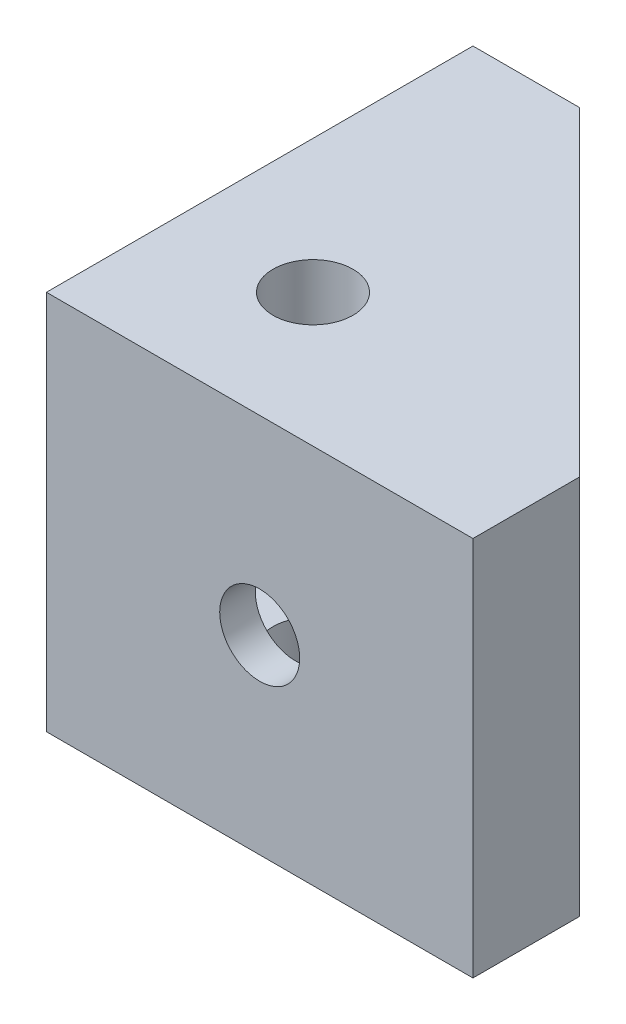
SolidWorks part; units mm, degrees
ref_plane "Front Plane" through (0, 0, 0) normal (0, 0, 1) x (1, 0, 0)
ref_plane "Top Plane" through (0, 0, 0) normal (0, 1, 0) x (1, 0, 0)
ref_plane "Right Plane" through (0, 0, 0) normal (1, 0, 0) x (0, 0, -1)
sketch "Sketch1" plane through (0, 0, 0) normal (0, 1, 0) x (1, 0, 0)
  line L1 (0, 0) -> (38.1, 0)
  line L5 (0, 0) -> (0, 38.1)
  line L6 (0, 38.1) -> (9.525, 38.1)
  line L7 (9.525, 38.1) -> (38.1, 9.525)
  line L8 (38.1, 9.525) -> (38.1, 0)
  dimension "D1" = 38.1
  dimension "D2" = 9.525
extrude "Main Body" add sketch "Sketch1" along normal blind 34
sketch "Sketch3" plane through (0, 0, 0) normal (0, 0, 1) x (1, 0, 0)
  line L0 (0, 0) -> (38.1, 34) construction
  circle A0 centre (19.05, 17) radius 3.5719
  circle A1 centre (19.05, 17) radius 7.9375 construction
  dimension "D1" = 7.1437
  dimension "D2" = 15.875
extrude "9/32 Right Rail" cut sketch "Sketch3" against normal through all both and the other way through all
sketch "Sketch4" plane through (0, 0, 0) normal (-1, 0, 0) x (0, 0, 1)
  line L0 (0, 0) -> (-38.1, 34) construction
  circle A0 centre (-19.05, 17) radius 3.5719
  circle A1 centre (-19.05, 17) radius 7.9375 construction
  dimension "D1" = 7.1437
  dimension "D2" = 15.875
extrude "9/32 Left Rail" cut sketch "Sketch4" against normal blind 34
ref_plane "Plane1" through (0, 27.65, 0) normal (0, 1, 0) x (1, 0, 0)
sketch "Sketch5" plane through (0, 27.65, 0) normal (0, 1, 0) x (1, 0, 0)
  line L1 (23.8125, 23.8125) -> (0, 0) construction
  line L2 (0, 38.1) -> (0, 0) construction
  line L5 (3.175, 28.3824) -> (11.2088, 36.4162)
  line L6 (38.1, 9.525) -> (9.525, 38.1) construction
  line L7 (11.2088, 36.4162) -> (36.4162, 11.2088)
  line L8 (36.4162, 11.2088) -> (28.3824, 3.175)
  line L9 (15.4781, 0) -> (22.6219, 0) construction
  line L15 (3.175, 28.3824) -> (3.175, 3.175)
  line L16 (3.175, 3.175) -> (28.3824, 3.175)
  line L20 (0, 22.6219) -> (0, 15.4781) construction
  line L21 (15.4781, 0) -> (22.6219, 0) construction
  line L22 (0, 22.6219) -> (0, 15.4781) construction
  dimension "D1" = 3.175
  dimension "D3" = 2.3812
extrude "Inner Hollow" cut sketch "Sketch5" against normal offset from surface (21.3 mm away) 6.35 up to face at (17.145, 0, -17.145)
sketch "Sketch6" plane through (0, 34, 0) normal (0, 1, 0) x (1, 0, 0)
  line L0 (23.8125, 23.8125) -> (0, 0) construction
  line L2 (38.1, 9.525) -> (9.525, 38.1) construction
  line L8 (36.4162, 11.2088) -> (11.2088, 36.4162)
  line L9 (28.3824, 3.175) -> (36.4162, 11.2088)
  line L10 (3.175, 3.175) -> (28.3824, 3.175)
  line L11 (3.175, 28.3824) -> (3.175, 3.175)
  line L12 (11.2088, 36.4162) -> (3.175, 28.3824)
  line L13 (36.4162, 11.2088) -> (11.2088, 36.4162) construction
  line L14 (28.3824, 3.175) -> (36.4162, 11.2088) construction
  line L15 (3.175, 3.175) -> (28.3824, 3.175) construction
  line L16 (3.175, 28.3824) -> (3.175, 3.175) construction
  line L17 (11.2088, 36.4162) -> (3.175, 28.3824) construction
  circle A1 centre (11.9063, 11.9063) radius 3.5719
  circle A2 centre (11.9063, 11.9063) radius 7.9375 construction
  dimension "D1" = 7.1437
  dimension "D3" = 15.875
  dimension "D2" = 0
extrude "9/32 Top Hole" cut sketch "Sketch6" against normal through all both and the other way through all
